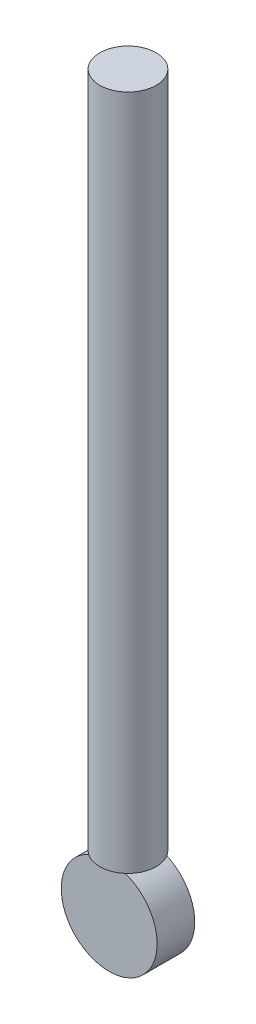
SolidWorks part; units mm, degrees
ref_plane "Front Plane" through (0, 0, 0) normal (0, 0, 1) x (1, 0, 0)
ref_plane "Top Plane" through (0, 0, 0) normal (0, 1, 0) x (1, 0, 0)
ref_plane "Right Plane" through (0, 0, 0) normal (1, 0, 0) x (0, 0, -1)
sketch "Sketch1" plane through (0, 0, 0) normal (0, 1, 0) x (1, 0, 0)
  circle A0 centre (0, 0) radius 9.525
  dimension "D1" = 19.05
extrude "Boss-Extrude1" add sketch "Sketch1" along normal blind 228.6
sketch "Sketch3" plane through (0, 0, 0) normal (0, 0, 1) x (1, 0, 0)
  circle A0 centre (0, -16.04) radius 16.198
extrude "Boss-Extrude2" add sketch "Sketch3" along normal mid plane 12.7
